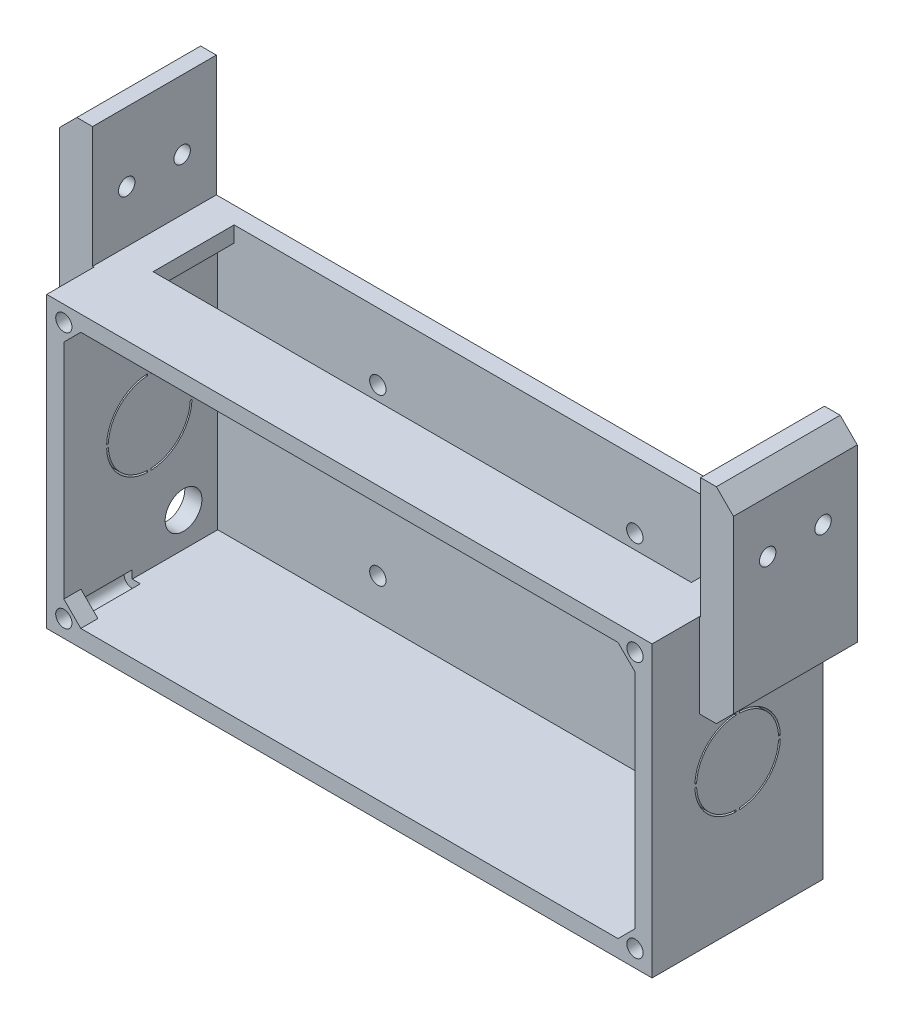
SolidWorks part; units mm, degrees
ref_plane "Front Plane" through (0, 0, 0) normal (0, 0, 1) x (1, 0, 0)
ref_plane "Top Plane" through (0, 0, 0) normal (0, 1, 0) x (1, 0, 0)
ref_plane "Right Plane" through (0, 0, 0) normal (1, 0, 0) x (0, 0, -1)
sketch "Sketch1" plane through (0, 0, 0) normal (0, 0, 1) x (1, 0, 0)
  line L1 (-88.5, -42.5) -> (88.5, -42.5)
  line L2 (-88.5, -42.5) -> (-88.5, 42.5)
  line L3 (-88.5, 42.5) -> (88.5, 42.5)
  line L4 (88.5, -42.5) -> (88.5, 42.5)
  line L5 (-88.5, -42.5) -> (88.5, 42.5) construction
  line L6 (-88.5, 42.5) -> (88.5, -42.5) construction
  point P0 (0, 0)
  dimension "D1" = 177
  dimension "D2" = 85
extrude "Boss-Extrude1" add sketch "Sketch1" along normal blind 50
shell "Shell1" thickness 5
sketch "Sketch2" plane through (0, 37.5, 0) normal (0, -1, 0) x (1, 0, 0)
  line L0 (78.7, 5) -> (-78.7, 5) construction
  line L1 (78.7, 28.7) -> (78.7, 5) construction
  line L2 (-78.7, 28.7) -> (78.7, 28.7) construction
  line L3 (-78.7, 5) -> (-78.7, 28.7) construction
  line L4 (78.7, 5) -> (-78.7, 5)
  line L5 (78.7, 28.7) -> (78.7, 5)
  line L6 (-78.7, 28.7) -> (78.7, 28.7)
  line L7 (-78.7, 5) -> (-78.7, 28.7)
extrude "Cut-Extrude1" cut sketch "Sketch2" against normal through all
sketch "Sketch4" plane through (-83.5, 0, 0) normal (1, 0, 0) x (0, 0, -1)
  line L0 (0, 42.5) -> (0, -42.5) construction
  line L1 (-50, -42.5) -> (0, -42.5) construction
  circle A0 centre (-15, -27.5) radius 5.375
  point P2 (0, 0)
  point P6 (-9.4162, -27.5)
  dimension "D3" = 10.75
  dimension "D2" = 15
  dimension "D4" = 15
extrude "Cut-Extrude2" cut sketch "Sketch4" against normal through all
sketch "Sketch6" plane through (0, 0, 50) normal (0, 0, 1) x (1, 0, 0)
  line L0 (87.0093, 41.0093) -> (75.0278, 41.0093)
  line L1 (83.5, 37.5) -> (-83.5, 37.5) construction
  line L2 (75.0278, 41.0093) -> (87.0093, 29.0278)
  line L3 (83.5, -37.5) -> (83.5, 37.5) construction
  line L4 (87.0093, 29.0278) -> (87.0093, 41.0093)
  line L5 (87.0093, 41.0093) -> (81.0185, 35.0185) construction
  line L6 (83.5, 0) -> (-83.5, 0) construction
  line L7 (-83.5, 37.5) -> (-83.5, -37.5) construction
  line L8 (0, 37.5) -> (0, -37.5) construction
  line L9 (-83.5, -37.5) -> (83.5, -37.5) construction
  line L10 (75.0278, -41.0093) -> (87.0093, -29.0278)
  line L11 (87.0093, -41.0093) -> (75.0278, -41.0093)
  line L12 (87.0093, -29.0278) -> (87.0093, -41.0093)
  line L13 (-87.0093, -41.0093) -> (-75.0278, -41.0093)
  line L14 (-87.0093, -29.0278) -> (-87.0093, -41.0093)
  line L15 (-75.0278, -41.0093) -> (-87.0093, -29.0278)
  line L16 (-75.0278, 41.0093) -> (-87.0093, 29.0278)
  line L17 (-87.0093, 41.0093) -> (-75.0278, 41.0093)
  line L18 (-87.0093, 29.0278) -> (-87.0093, 41.0093)
  line L19 (88.5, 42.5) -> (-88.5, 42.5) construction
  line L21 (88.5, -42.5) -> (88.5, 42.5) construction
  circle A0 centre (83.5, 37.5) radius 2.375
  circle A1 centre (83.5, 37.5) radius 3.5093 construction
  circle A2 centre (83.5, -37.5) radius 2.375
  circle A3 centre (-83.5, -37.5) radius 2.375
  circle A4 centre (-83.5, 37.5) radius 2.375
  dimension "D2" = 4.75
  dimension "D1" = 11.9815
  dimension "D3" = 5
  dimension "D4" = 5
extrude "Boss-Extrude3" add sketch "Sketch6" against normal blind 5
sketch "Sketch7" plane through (0, 0, 50) normal (0, 0, 1) x (1, 0, 0)
  circle A0 centre (83.5, 37.5) radius 2.375
  arc A1 (81.125, 37.5) -> (83.5, 35.125) centre (83.5, 37.5) ccw construction
  circle A2 centre (83.5, -37.5) radius 2.375
  arc A3 (83.5, -35.125) -> (81.125, -37.5) centre (83.5, -37.5) ccw construction
  circle A4 centre (-83.5, -37.5) radius 2.375
  arc A5 (-81.125, -37.5) -> (-83.5, -35.125) centre (-83.5, -37.5) ccw construction
  circle A6 centre (-83.5, 37.5) radius 2.375
  arc A7 (-83.5, 35.125) -> (-81.125, 37.5) centre (-83.5, 37.5) ccw construction
extrude "Cut-Extrude4" cut sketch "Sketch7" against normal blind 20
sketch "Sketch8" plane through (0, 0, 0) normal (0, 0, -1) x (-1, 0, 0)
  line L0 (-88.5, -42.5) -> (-88.5, 42.5) construction
  line L1 (-88.5, 17.5) -> (-98.5, 17.5)
  line L2 (-88.5, 17.5) -> (-88.5, 77.5)
  line L3 (-88.5, 77.5) -> (-98.5, 77.5)
  line L4 (-98.5, 17.5) -> (-98.5, 77.5)
  line L5 (88.5, 42.5) -> (88.5, -42.5) construction
  line L6 (88.5, 17.5) -> (98.5, 17.5)
  line L7 (88.5, 17.5) -> (88.5, 77.5)
  line L8 (88.5, 77.5) -> (98.5, 77.5)
  line L9 (98.5, 17.5) -> (98.5, 77.5)
  line L10 (-88.5, 42.5) -> (88.5, 42.5) construction
  dimension "D1" = 10
  dimension "D2" = 60
  dimension "D3" = 25
extrude "Boss-Extrude4" add sketch "Sketch8" against normal blind 36.2
chamfer "Chamfer1" distance 5 angle 45 4 edges at (-98.5, 17.5, 18.1) (-98.5, 77.5, 18.1) (98.5, 77.5, 18.1) (98.5, 17.5, 18.1)
sketch "Sketch9" plane through (0, 0, 0) normal (0, 0, -1) x (-1, 0, 0)
  line L0 (-88.9, 42.1) -> (-88.9, 77.9)
  line L1 (-88.5, 42.5) -> (88.5, 42.5)
  line L2 (-88.5, 42.5) -> (-88.5, 77.5)
  line L3 (-88.5, 77.5) -> (88.5, 77.5)
  line L4 (88.5, 42.5) -> (88.5, 77.5)
  line L5 (-88.9, 77.9) -> (88.9, 77.9)
  line L6 (88.9, 42.1) -> (88.9, 77.9)
  line L7 (-88.9, 42.1) -> (88.9, 42.1)
  dimension "D1" = 0.4
extrude "Cut-Extrude5" cut sketch "Sketch9" against normal through all
sketch "Sketch10" plane through (-98.5, 0, 0) normal (1, 0, 0) x (0, 0, -1)
  line L0 (-36.2, 57.3) -> (-26.2, 57.3) construction
  line L1 (-36.2, 72.5) -> (0, 72.5) construction
  line L2 (-36.2, 72.5) -> (-36.2, 42.1) construction
  line L3 (-36.2, 42.1) -> (0, 42.1) construction
  line L4 (-36.2, 77.5) -> (-36.2, 72.5)
  line L5 (0, 77.5) -> (-36.2, 77.5)
  line L6 (0, 72.5) -> (0, 77.5)
  line L7 (-36.2, 72.5) -> (0, 72.5)
  line L8 (-36.2, 77.5) -> (-36.2, 72.5) construction
  line L9 (0, 77.5) -> (-36.2, 77.5) construction
  line L10 (0, 72.5) -> (0, 77.5) construction
  line L11 (-36.2, 72.5) -> (0, 72.5) construction
  line L12 (0, 72.5) -> (0, 42.1) construction
  line L13 (-26.2, 57.3) -> (-10, 57.3) construction
  line L14 (-10, 57.3) -> (0, 57.3) construction
  circle A0 centre (-26.2, 57.3) radius 2.4
  circle A1 centre (-10, 57.3) radius 2.4
  dimension "D2" = 4.8
  dimension "D3" = 10
  dimension "D1" = 0
extrude "Cut-Extrude6" cut sketch "Sketch10" along normal through all
sketch "Sketch11" plane through (0, 0, 5) normal (0, 0, 1) x (1, 0, 0)
  circle A0 centre (45.9486, -25.7387) radius 1.5621 construction
  circle A1 centre (-36.6776, -25.7387) radius 1.5621 construction
  circle A2 centre (-36.6776, 22.5975) radius 1.5621 construction
  circle A3 centre (38.4556, 22.5975) radius 1.5621 construction
  circle A4 centre (45.9486, -25.7387) radius 1.5621 construction
  circle A5 centre (-36.6776, -25.7387) radius 1.5621 construction
  circle A6 centre (-36.6776, 22.5975) radius 1.5621 construction
  circle A7 centre (38.4556, 22.5975) radius 1.5621 construction
  circle A8 centre (45.9486, -25.7387) radius 2.4
  circle A9 centre (38.4556, 22.5975) radius 2.4
  circle A10 centre (-36.6776, 22.5975) radius 2.4
  circle A11 centre (-36.6776, -25.7387) radius 2.4
  dimension "D1" = 4.8
extrude "Cut-Extrude8" cut sketch "Sketch11" against normal up to surface (5 mm away) up to face at (0, 35.575, 0)
sketch "Sketch12" plane through (-88.5, 0, 0) normal (-1, 0, 0) x (0, 0, 1)
  line L2 (12.5, -0.2) -> (13, -0.2) construction
  line L3 (25.5, 12.3104) -> (24.5, 12.3104)
  line L4 (12.4896, 0.3) -> (13.0104, 0.3)
  line L5 (12.4896, 0.3) -> (12.4896, -0.7)
  line L6 (12.4896, -0.7) -> (13.0104, -0.7)
  line L7 (13.0104, 0.3) -> (13.0104, -0.7)
  line L8 (12.4896, 0.3) -> (13.0104, -0.7) construction
  line L9 (12.4896, -0.7) -> (13.0104, 0.3) construction
  line L10 (25.5, 12.3104) -> (25.5, 11.7896)
  line L11 (25.5, 11.7896) -> (24.5, 11.7896)
  line L12 (24.5, 12.3104) -> (24.5, 11.7896)
  line L13 (37.5104, -0.7) -> (37.5104, 0.3)
  line L14 (37.5104, -0.7) -> (36.9896, -0.7)
  line L15 (36.9896, -0.7) -> (36.9896, 0.3)
  line L16 (37.5104, 0.3) -> (36.9896, 0.3)
  line L17 (24.5, -12.7104) -> (25.5, -12.7104)
  line L18 (24.5, -12.7104) -> (24.5, -12.1896)
  line L19 (24.5, -12.1896) -> (25.5, -12.1896)
  line L20 (25.5, -12.7104) -> (25.5, -12.1896)
  line L21 (25, 42.1) -> (25, -42.5) construction
  line L22 (50, -42.5) -> (0, -42.5) construction
  line L23 (50, 42.1) -> (36.2, 42.1) construction
  circle A0 centre (25, -0.2) radius 12.5
  circle A2 centre (25, -0.2) radius 12
  point P3 (25, -42.5)
  point P8 (12.75, -0.2)
  point P16 (22.1251, 42.3)
  point P17 (22.1251, 30.4932)
  point P35 (25, -0.2)
  dimension "D2" = 25
  dimension "D5" = 1
  dimension "D4" = 0.5
  dimension "D6" = 4
extrude "Cut-Extrude14" cut sketch "Sketch12" against normal through all contours A2 L12 A0 L4 | A2 L6 A0 L18 | A2 L20 A0 L14 | A2 L16 A0 L10
